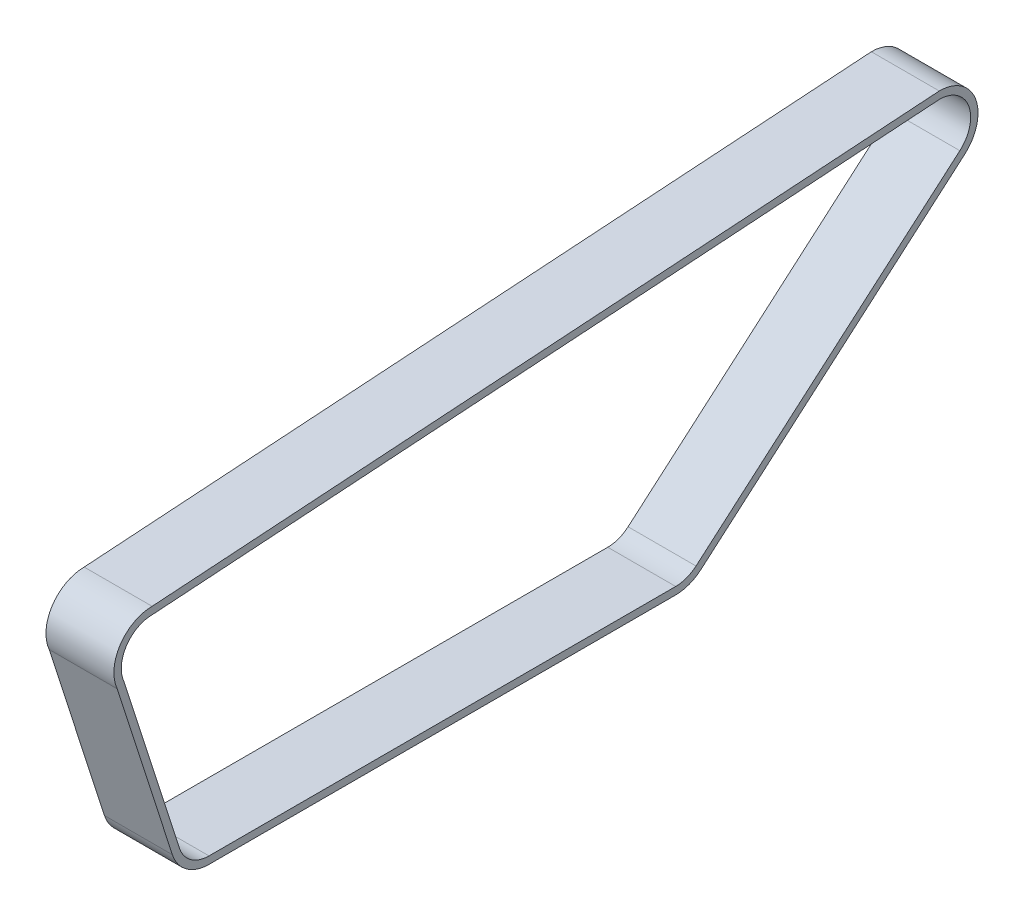
SolidWorks part; units mm, degrees
ref_plane "前视基准面" through (0, 0, 0) normal (0, 0, 1) x (1, 0, 0)
ref_plane "上视基准面" through (0, 0, 0) normal (0, 1, 0) x (1, 0, 0)
ref_plane "右视基准面" through (0, 0, 0) normal (1, 0, 0) x (0, 0, -1)
sketch "草图1" plane through (0, 0, 0) normal (-1, 0, 0) x (0, 0, 1)
  line L66 (-259.7095, 653.4477) -> (-98.548, 514.3298)
  line L67 (250.8162, 627.7582) -> (217.0092, 522.883)
  line L69 (-86.1326, 509.7124) -> (198.9255, 509.7124)
  line L70 (-247.2942, 686.8303) -> (233.527, 654.6375)
  line L71 (-247.1357, 691.3297) -> (233.6854, 659.137)
  line L72 (255.0234, 626.1426) -> (221.2922, 521.5024)
  line L73 (-86.1326, 505.2124) -> (198.9255, 505.2124)
  line L74 (-262.65, 650.0413) -> (-101.4884, 510.9234)
  arc A256 (250.8162, 627.7582) -> (233.527, 654.6375) centre (233.527, 635.6375) ccw
  arc A257 (-98.548, 514.3298) -> (-86.1326, 509.7124) centre (-86.1326, 528.7124) ccw
  arc A258 (-247.2942, 686.8303) -> (-259.7095, 653.4477) centre (-247.2942, 667.8303) ccw
  arc A259 (198.9255, 509.7124) -> (217.0092, 522.883) centre (198.9255, 528.7124) ccw
  arc A260 (255.0234, 626.1426) -> (233.6854, 659.137) centre (233.527, 635.6375) ccw
  arc A261 (198.9255, 505.2124) -> (221.2922, 521.5024) centre (198.9255, 528.7124) ccw
  arc A262 (-101.4884, 510.9234) -> (-86.1326, 505.2124) centre (-86.1326, 528.7124) ccw
  arc A263 (-247.1357, 691.3297) -> (-262.65, 650.0413) centre (-247.2942, 667.8303) ccw
  point P0 (-150, 0)
  point P1 (135, 0)
  point P9 (-344.9533, 138.7825)
  point P10 (187.1329, 101.1747)
  point P11 (165.9429, -19)
  point P12 (-156.9154, -19)
  dimension "D28" = 4.5
  dimension "D27" = 38
extrude "凸台-拉伸1" add sketch "草图1" along normal blind 41.5
